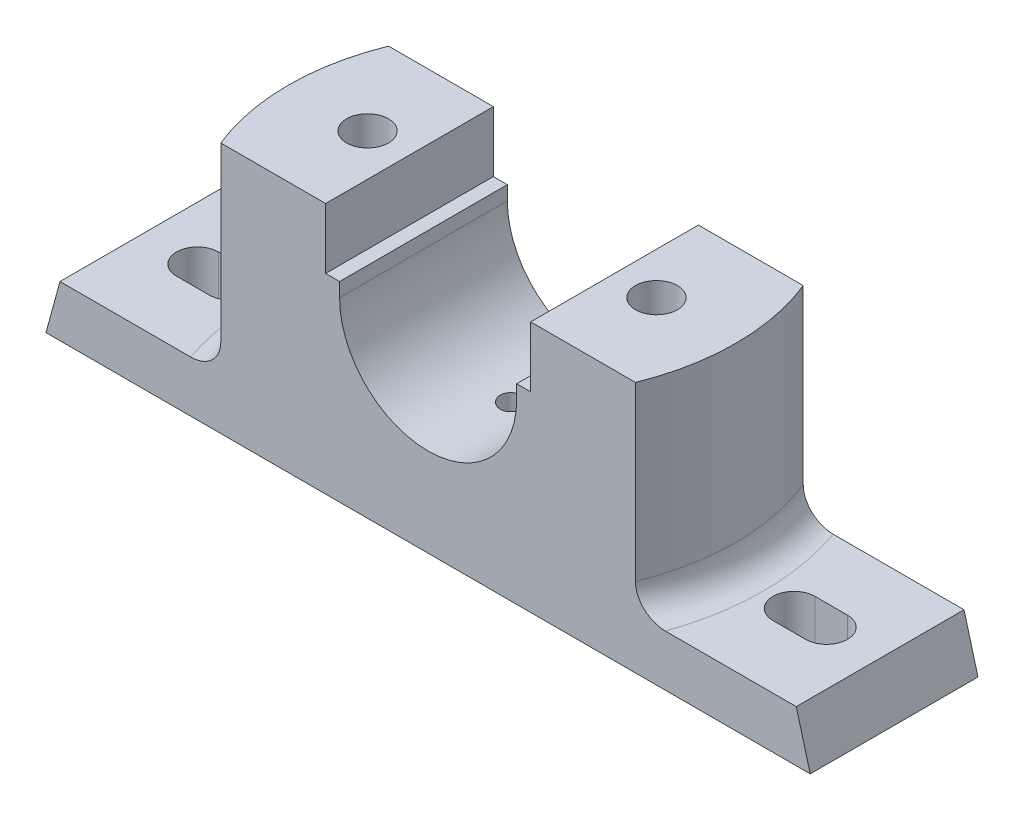
SolidWorks part; units mm, degrees
ref_plane "Front Plane" through (0, 0, 0) normal (0, 0, 1) x (1, 0, 0)
ref_plane "Top Plane" through (0, 0, 0) normal (0, 1, 0) x (1, 0, 0)
ref_plane "Right Plane" through (0, 0, 0) normal (1, 0, 0) x (0, 0, -1)
sketch "Sketch1" plane through (0, 0, 0) normal (0, 0, 1) x (1, 0, 0)
  line L0 (0, 57.1369) -> (0, -64.9031) construction
  line L1 (-82, -43.8235) -> (82, -43.8235)
  line L2 (82, -43.8235) -> (79, -32.8235)
  line L3 (79, -32.8235) -> (50, -32.8235)
  line L4 (50, -32.8235) -> (50, 10.1765)
  line L5 (50, 10.1765) -> (22, 10.1765)
  line L6 (22, 10.1765) -> (22, -2.8235)
  line L7 (22, -2.8235) -> (19, -2.8235)
  line L8 (19, -2.8235) -> (19, -5.8235)
  line L9 (-82, -43.8235) -> (-79, -32.8235)
  line L10 (-79, -32.8235) -> (-50, -32.8235)
  line L11 (-50, -32.8235) -> (-50, 10.1765)
  line L12 (-50, 10.1765) -> (-22, 10.1765)
  line L13 (-22, 10.1765) -> (-22, -2.8235)
  line L14 (-22, -2.8235) -> (-19, -2.8235)
  line L15 (-19, -2.8235) -> (-19, -5.8235)
  arc A0 (19, -5.8235) -> (-19, -5.8235) centre (0, -5.8235) cw
  point P5 (0, -5.8235)
  point P16 (0, -43.8235)
  point P24 (-124.3296, -42.1072)
  point P25 (0, 0)
  point P26 (-18.8869, 8.783)
  dimension "D1" = 3
  dimension "D2" = 11
  dimension "D3" = 164
  dimension "D4" = 0
  dimension "D5" = 38
  dimension "D6" = 100
  dimension "D7" = 44
  dimension "D8" = 3
  dimension "D9" = 16
  dimension "D10" = 54
extrude "Boss-Extrude3" add sketch "Sketch1" along normal mid plane 36
sketch "Sketch3" plane through (0, 10.1765, 0) normal (0, 1, 0) x (1, 0, 0)
  line L4 (-22, 18) -> (-50, 18)
  line L5 (-50, 18) -> (-50, -18)
  line L6 (-50, -18) -> (-22, -18)
  line L7 (-22, -18) -> (-22, 18)
  line L8 (-44.4972, 18) -> (-50, 18)
  line L9 (-50, 18) -> (-50, -18)
  line L10 (-50, -18) -> (-44.4972, -18)
  arc A0 (-44.4972, 18) -> (-44.4972, -18) centre (0, 0) ccw
  dimension "D2" = 48
  dimension "D1" = 0
extrude "Cut-Extrude1" cut sketch "Sketch3" against normal up to surface (43 mm away) up to face at (-64.5, -32.8235, 0)
mirror "Mirror1" about plane through (0, 0, 0) normal (1, 0, 0) of "Cut-Extrude1"
hole_wizard "M6 Tapped Hole1" positions "3DSketch2" profile "Sketch5" tap size "M6" standard "ISO"
sketch3d "3DSketch2"
  point P0 (0, -24.8235, 0)
  dimension "D1" = 0
  dimension "D2" = 0
sketch "Sketch5" plane through (0, -24.8235, 0) normal (1, 0, 0) x (0, 0, 1)
  line L0 (0, 0) -> (0, 7.5022)
  line L1 (0, 7.5022) -> (2.5, 6)
  line L2 (2.5, 6) -> (2.5, 0)
  line L5 (2.5, 0) -> (0, 0)
  line L10 (0, 7.5022) -> (-2.5, 6) construction
  line L11 (0, -6.35) -> (0, 107.95) construction
  dimension "Tap Drill Dia." = 5
  dimension "Tap Drill Depth" = 6
  dimension "Drill Angle" = 118
cosmetic thread "Hole Thread1"
hole_wizard "M10 Tapped Hole1" positions "Sketch7" profile "Sketch8" tap size "M10" standard "ISO" end condition through all
sketch "Sketch7" plane through (0, 10.1765, 0) normal (0, 1, 0) x (1, 0, 0)
  line L0 (0, -19.8) -> (0, 19.8) construction
  point P0 (-31, 0)
  dimension "D1" = 31
sketch "Sketch8" plane through (-31, 10.1765, 0) normal (1, 0, 0) x (0, 0, 1)
  line L0 (0, 0) -> (0, 54)
  line L1 (0, 54) -> (4.5, 54)
  line L2 (4.5, 54) -> (4.5, 0)
  line L5 (4.5, 0) -> (0, 0)
  line L11 (0, -6.35) -> (0, 107.95) construction
  dimension "Thru Tap Drill Dia." = 9
  dimension "Thru Tap Drill Depth" = 54
cosmetic thread "Hole Thread2"
sketch "Sketch9" plane through (0, -43.8235, 0) normal (0, -1, 0) x (1, 0, 0)
  line L1 (-41, 10) -> (-21, 10)
  line L2 (-41, 10) -> (-41, -10)
  line L3 (-41, -10) -> (-21, -10)
  line L4 (-21, 10) -> (-21, -10)
  line L5 (-41, 10) -> (-21, -10) construction
  line L6 (-41, -10) -> (-21, 10) construction
  point P0 (-31, 0)
  dimension "D1" = 20
extrude "Cut-Extrude2" cut sketch "Sketch9" against normal blind 8
sketch "Sketch10" plane through (0, -43.8235, 0) normal (0, -1, 0) x (1, 0, 0)
  line L0 (-67.5, 0) -> (-60.5, 0) construction
  line L1 (-67.5, 4.5) -> (-60.5, 4.5)
  line L2 (-67.5, -4.5) -> (-60.5, -4.5)
  arc A0 (-67.5, 4.5) -> (-67.5, -4.5) centre (-67.5, 0) ccw
  arc A1 (-60.5, -4.5) -> (-60.5, 4.5) centre (-60.5, 0) ccw
  point P2 (-64, 0)
  dimension "D1" = 16
  dimension "D2" = 9
  dimension "D3" = 64
extrude "Cut-Extrude3" cut sketch "Sketch10" against normal up to next (11 mm away)
mirror "Mirror2" about plane through (0, 0, 0) normal (1, 0, 0) of "Cut-Extrude3", "Cut-Extrude2", "M10 Tapped Hole1"
fillet "Fillet2" radius 6 1 edges at (-48, -32.8235, 0)
fillet "Fillet3" radius 6 1 edges at (48, -32.8235, 0)
